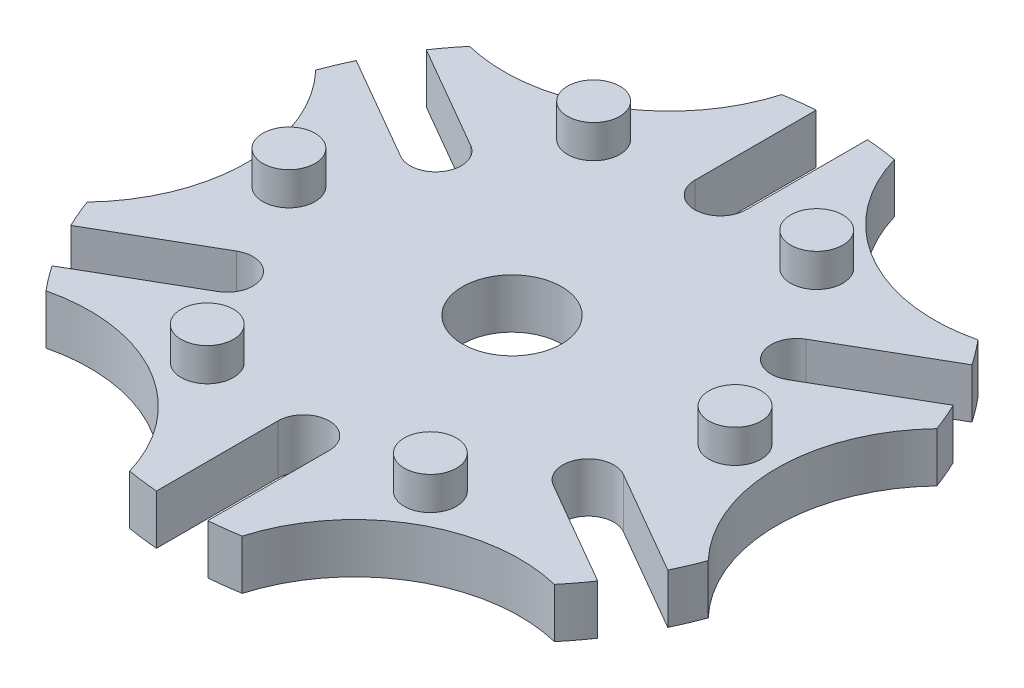
SolidWorks part; units mm, degrees
ref_plane "Front Plane" through (0, 0, 0) normal (0, 0, 1) x (1, 0, 0)
ref_plane "Top Plane" through (0, 0, 0) normal (0, 1, 0) x (1, 0, 0)
ref_plane "Right Plane" through (0, 0, 0) normal (1, 0, 0) x (0, 0, -1)
sketch "Sketch1" plane through (0, 0, 0) normal (0, 1, 0) x (1, 0, 0)
  line L0 (7.75, 63) -> (7.75, 99.6992)
  line L1 (-7.75, 63) -> (-7.75, 99.6992)
  line L2 (50.6846, 38.2117) -> (82.4671, 56.5613)
  line L3 (58.4346, 24.7883) -> (90.2171, 43.1379)
  line L4 (58.4346, -24.7883) -> (90.2171, -43.1379)
  line L5 (50.6846, -38.2117) -> (82.4671, -56.5613)
  line L6 (7.75, -63) -> (7.75, -99.6992)
  line L7 (-7.75, -63) -> (-7.75, -99.6992)
  line L8 (-50.6846, -38.2117) -> (-82.4671, -56.5613)
  line L9 (-58.4346, -24.7883) -> (-90.2171, -43.1379)
  line L10 (-58.4346, 24.7883) -> (-90.2171, 43.1379)
  line L11 (-50.6846, 38.2117) -> (-82.4671, 56.5613)
  line L12 (0, 0) -> (-130, 0) construction
  arc A0 (-76.8342, 64.004) -> (-82.4671, 56.5613) centre (0, 0) ccw
  circle A1 centre (0, 0) radius 15
  circle A2 centre (0, 63) radius 7.75
  circle A3 centre (54.5596, 31.5) radius 7.75
  circle A4 centre (54.5596, -31.5) radius 7.75
  circle A5 centre (0, -63) radius 7.75
  circle A6 centre (-54.5596, -31.5) radius 7.75
  circle A7 centre (-54.5596, 31.5) radius 7.75
  arc A8 (-93.8462, 34.5384) -> (-93.8462, -34.5384) centre (-130, 0) cw
  arc A9 (-17.012, 98.5423) -> (-76.8342, 64.004) centre (-65, 112.5833) cw
  arc A10 (76.8342, 64.004) -> (17.012, 98.5423) centre (65, 112.5833) cw
  arc A11 (93.8462, -34.5384) -> (93.8462, 34.5384) centre (130, 0) cw
  arc A12 (17.012, -98.5423) -> (76.8342, -64.004) centre (65, -112.5833) cw
  arc A13 (-76.8342, -64.004) -> (-17.012, -98.5423) centre (-65, -112.5833) cw
  arc A14 (-90.2171, 43.1379) -> (-93.8462, 34.5384) centre (0, 0) ccw
  arc A15 (-93.8462, -34.5384) -> (-90.2171, -43.1379) centre (0, 0) ccw
  arc A16 (-82.4671, -56.5613) -> (-76.8342, -64.004) centre (0, 0) ccw
  arc A17 (-17.012, -98.5423) -> (-7.75, -99.6992) centre (0, 0) ccw
  arc A18 (7.75, -99.6992) -> (17.012, -98.5423) centre (0, 0) ccw
  arc A19 (76.8342, -64.004) -> (82.4671, -56.5613) centre (0, 0) ccw
  arc A20 (90.2171, -43.1379) -> (93.8462, -34.5384) centre (0, 0) ccw
  arc A21 (93.8462, 34.5384) -> (90.2171, 43.1379) centre (0, 0) ccw
  arc A22 (82.4671, 56.5613) -> (76.8342, 64.004) centre (0, 0) ccw
  arc A23 (17.012, 98.5423) -> (7.75, 99.6992) centre (0, 0) ccw
  arc A24 (-7.75, 99.6992) -> (-17.012, 98.5423) centre (0, 0) ccw
  point P42 (0, 0)
  point P61 (0, 0)
  dimension "D1" = 200
  dimension "D2" = 30
  dimension "D3" = 15.5
  dimension "D6" = 50
  dimension "D4" = 37
  dimension "D7" = 130
  dimension "D5" = 6
  dimension "D8" = 6
extrude "Boss-Extrude1" add sketch "Sketch1" along normal mid plane 15
sketch "Sketch2" plane through (0, 7.5, 0) normal (0, 1, 0) x (1, 0, 0)
  line L0 (-156.3617, 0) -> (216.5334, 0) construction
  line L1 (-78.1809, 135.4132) -> (108.2667, -187.5235) construction
  line L2 (78.1809, 135.4132) -> (-108.2667, -187.5235) construction
  line L3 (156.3617, 0) -> (-216.5334, 0) construction
  line L4 (78.1809, -135.4132) -> (-108.2667, 187.5235) construction
  line L5 (-78.1809, -135.4132) -> (108.2667, 187.5235) construction
  circle A0 centre (33.7097, 58.3869) radius 7.9008
  circle A1 centre (67.4194, 0) radius 7.9008
  circle A2 centre (33.7097, -58.3869) radius 7.9008
  circle A3 centre (-33.7097, -58.3869) radius 7.9008
  circle A4 centre (-67.4194, 0) radius 7.9008
  circle A5 centre (-33.7097, 58.3869) radius 7.9008
  point P16 (0, 0)
  point P29 (0, 0)
  dimension "D1" = 6
  dimension "D2" = 6
extrude "Boss-Extrude2" add sketch "Sketch2" along normal blind 10
